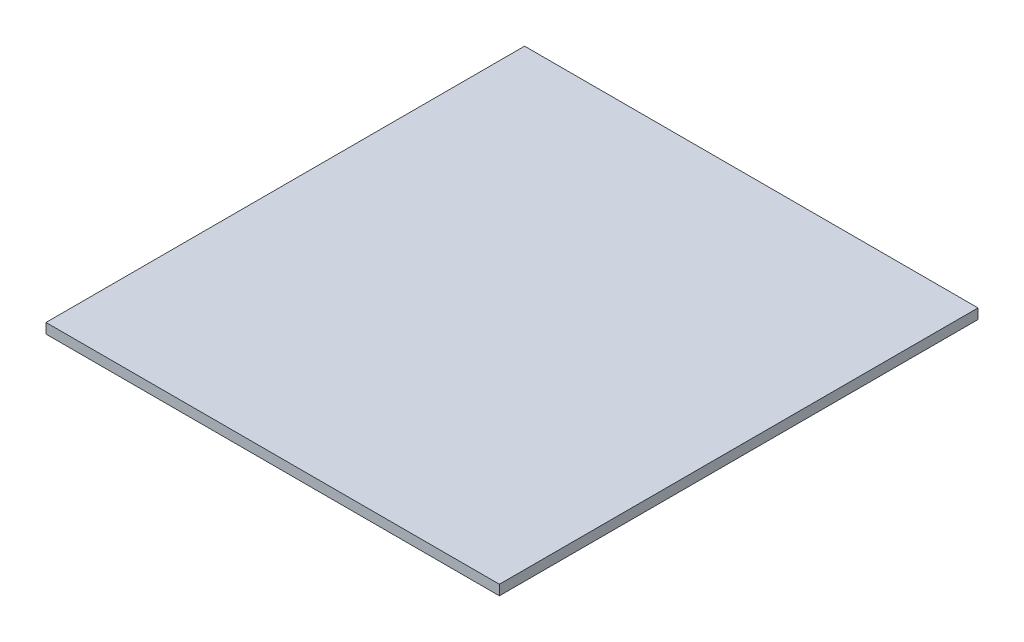
SolidWorks part; units mm, degrees
ref_plane "Plano frontal" through (0, 0, 0) normal (0, 0, 1) x (1, 0, 0)
ref_plane "Plano superior" through (0, 0, 0) normal (0, 1, 0) x (1, 0, 0)
ref_plane "Plano direito" through (0, 0, 0) normal (1, 0, 0) x (0, 0, -1)
sketch "Esboço1" plane through (0, 0, 0) normal (0, 0, 1) x (1, 0, 0)
  line L0 (89.875, 2.2917) -> (89.875, -14.8602) construction
  line L1 (0, 4) -> (180, 4)
  line L2 (0, 4) -> (0, 0)
  line L3 (0, 0) -> (180, 0)
  line L4 (180, 4) -> (180, 0)
  line L5 (-5.125, 0.2917) -> (232.21, 0.2917) construction
  dimension "D1" = 4
  dimension "D2" = 180
extrude "Ressalto-extrusão1" add sketch "Esboço1" along normal blind 190
